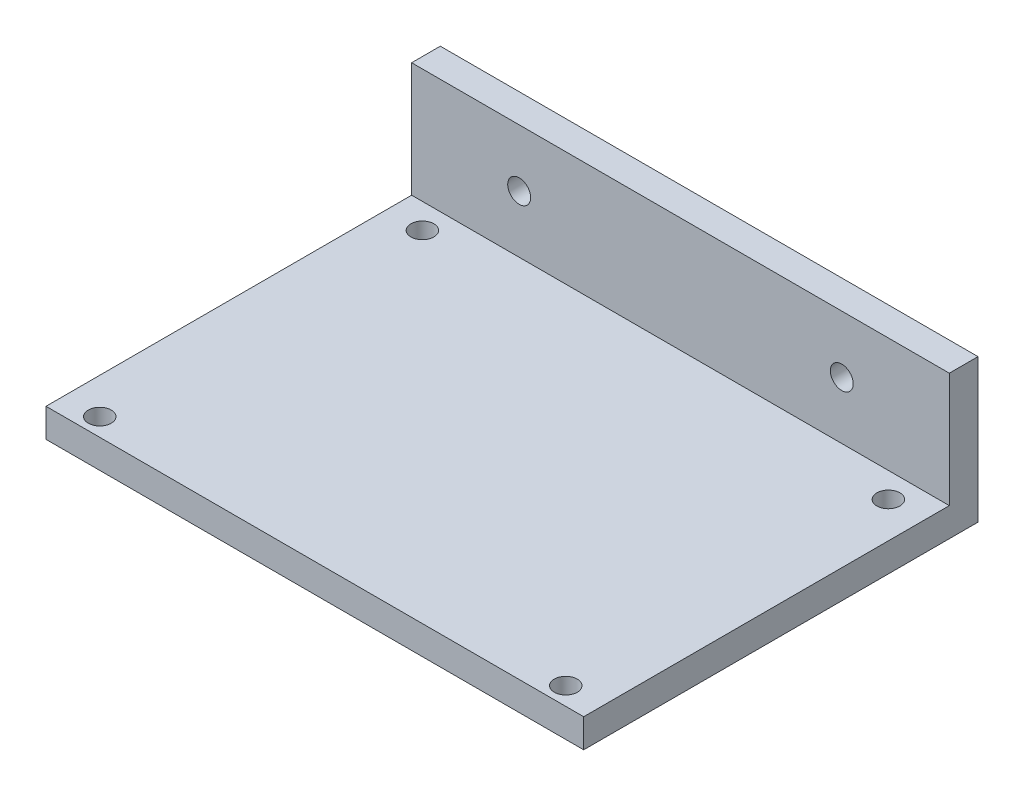
SolidWorks part; units mm, degrees
ref_plane "Front Plane" through (0, 0, 0) normal (0, 0, 1) x (1, 0, 0)
ref_plane "Top Plane" through (0, 0, 0) normal (0, 1, 0) x (1, 0, 0)
ref_plane "Right Plane" through (0, 0, 0) normal (1, 0, 0) x (0, 0, -1)
sketch "Sketch1" plane through (0, 0, 0) normal (0, 1, 0) x (1, 0, 0)
  line L1 (0, 0) -> (75, 0)
  line L2 (0, 0) -> (0, 55)
  line L3 (0, 55) -> (75, 55)
  line L4 (75, 0) -> (75, 55)
  dimension "D1" = 55
  dimension "D2" = 75
extrude "Boss-Extrude1" add sketch "Sketch1" along normal blind 20
sketch "Sketch2" plane through (75, 0, 0) normal (1, 0, 0) x (0, 0, -1)
  line L1 (0, 20) -> (51, 20)
  line L2 (0, 20) -> (0, 4)
  line L3 (0, 4) -> (51, 4)
  line L4 (51, 20) -> (51, 4)
  dimension "D1" = 16
  dimension "D2" = 51
extrude "Cut-Extrude1" cut sketch "Sketch2" against normal blind 94
sketch "Sketch3" plane through (0, 0, -55) normal (0, 0, -1) x (-1, 0, 0)
  line L0 (-75, 20) -> (0, 20) construction
  line L1 (-75, 20) -> (-75, 0) construction
  line L2 (0, 20) -> (0, 0) construction
  circle A0 centre (-60, 12) radius 1.6
  circle A1 centre (-15, 12) radius 1.6
  dimension "D1" = 3.2
  dimension "D2" = 3.2
  dimension "D3" = 8
  dimension "D4" = 8
  dimension "D5" = 15
  dimension "D6" = 15
extrude "Cut-Extrude2" cut sketch "Sketch3" against normal blind 54
sketch "Sketch4" plane through (0, 0, 0) normal (0, -1, 0) x (1, 0, 0)
  line L2 (0, -55) -> (0, 0) construction
  line L3 (75, -55) -> (0, -55) construction
  circle A0 centre (5, -2.5) radius 1.6
  circle A1 centre (5, -47.5) radius 1.6
  circle A2 centre (70, -47.5) radius 1.6
  circle A3 centre (70, -2.5) radius 1.6
  dimension "D1" = 3.2
  dimension "D2" = 3.2
  dimension "D3" = 3.2
  dimension "D4" = 3.2
  dimension "D5" = 45
  dimension "D6" = 65
  dimension "D7" = 45
  dimension "D8" = 65
  dimension "D9" = 5
  dimension "D10" = 7.5
  dimension "D11" = 5
  dimension "D12" = 7.5
extrude "Cut-Extrude3" cut sketch "Sketch4" against normal blind 10
